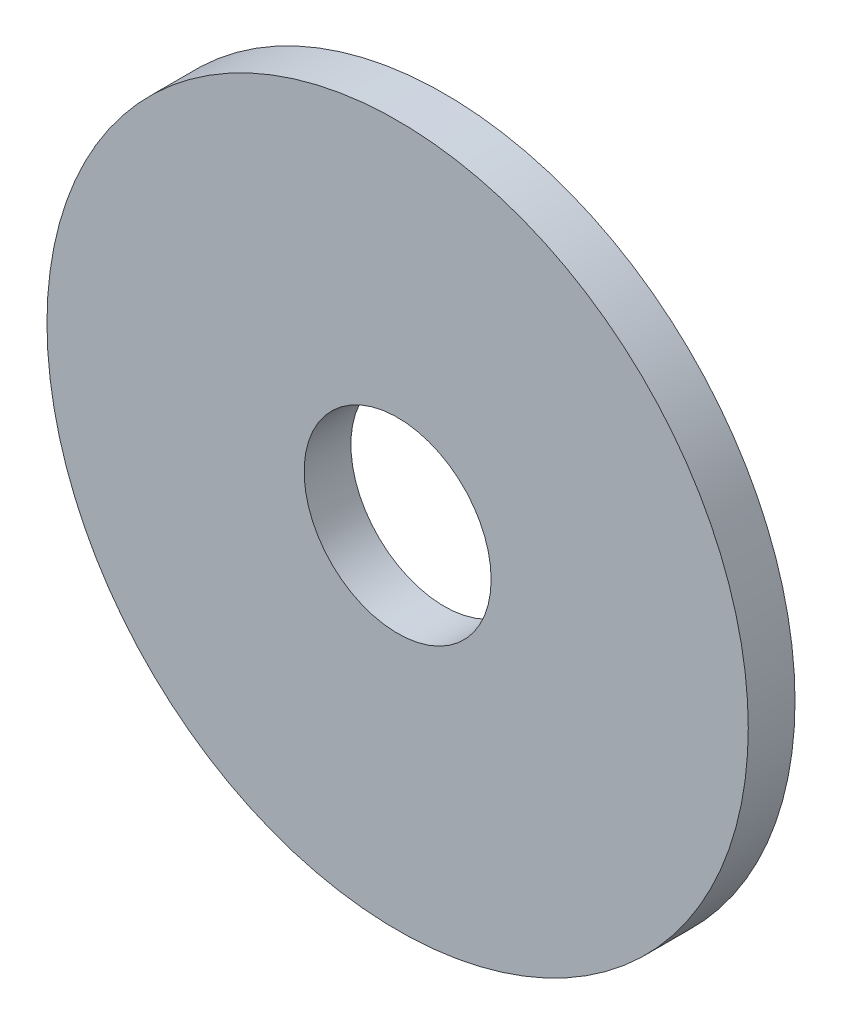
SolidWorks part; units mm, degrees
ref_plane "Plan1" through (0, 0, 0) normal (0, 0, 1) x (1, 0, 0)
ref_plane "Plan2" through (0, 0, 0) normal (0, 1, 0) x (1, 0, 0)
ref_plane "Plan3" through (0, 0, 0) normal (1, 0, 0) x (0, 0, -1)
sketch "Esquisse1" plane through (0, 0, 0) normal (0, 0, 1) x (1, 0, 0)
  circle A0 centre (0, 0) radius 4
  circle A1 centre (0, 0) radius 15
  dimension "D1" = 30
  dimension "D2" = 8
extrude "Base-Extrusion" add sketch "Esquisse1" along normal blind 2
